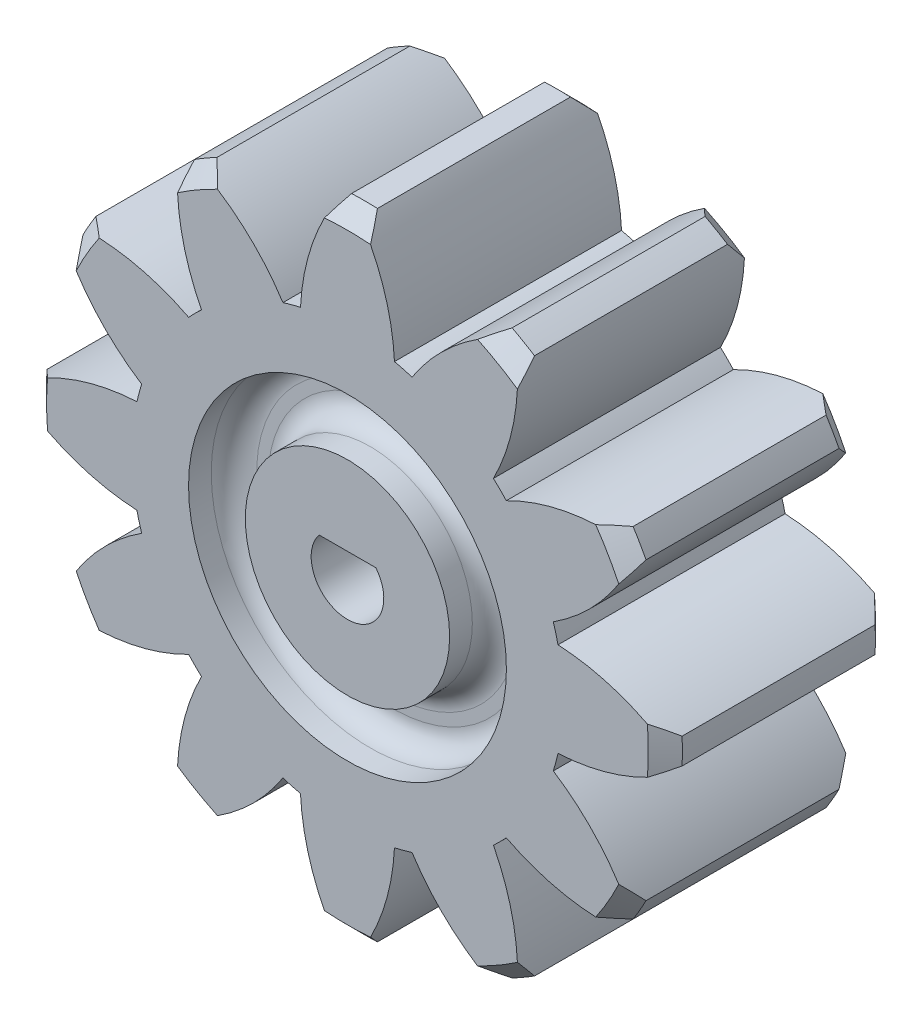
SolidWorks part; units mm, degrees
ref_plane "Front Plane" through (0, 0, 0) normal (0, 0, 1) x (1, 0, 0)
ref_plane "Top Plane" through (0, 0, 0) normal (0, 1, 0) x (1, 0, 0)
ref_plane "Right Plane" through (0, 0, 0) normal (1, 0, 0) x (0, 0, -1)
sketch "Sketch1" plane through (0, 0, 0) normal (0, 0, 1) x (1, 0, 0)
  line L0 (0, 18.2844) -> (0, -18.5063) construction
  line L1 (-21.4042, 0) -> (32.7718, 0) construction
  line L2 (-1.57, 17.3282) -> (-1.57, 3.0678) construction
  line L3 (-0.57, 19.83) -> (-0.57, 2.7238) construction
  line L4 (-2.07, 15.9554) -> (-2.07, 3.2392) construction
  circle A0 centre (0, 0) radius 9.5
  circle A1 centre (0, 0) radius 12 construction
  circle A2 centre (0, 0) radius 14
  arc A3 (-2.07, 9.2717) -> (-0.57, 13.9884) centre (7.6252, 8.7853) cw
  arc A4 (2.07, 9.2717) -> (0.57, 13.9884) centre (-7.6252, 8.7853) ccw
  point P18 (-1.57, 11.8969)
  dimension "D1" = 19
  dimension "D2" = 24
  dimension "D3" = 28
  dimension "D4" = 1.57
  dimension "D5" = 1
  dimension "D6" = 0.5
extrude "Boss-Extrude1" add sketch "Sketch1" along normal blind 10 contours A0 | A0 A4 A2 A3
chamfer "Chamfer1" distance 0.75 angle 45 2 edges at (0, 14, 0) (0, 14, 10)
pattern_circular "CirPattern1" count 12 over 360 about axis through (0, 0, 0) along (0, 0, 1) of "Boss-Extrude1", "Chamfer1"
sketch "Sketch2" plane through (0, 0, 10) normal (0, 0, 1) x (1, 0, 0)
  circle A0 centre (0, 0) radius 7
  circle A1 centre (0, 0) radius 4.5
  dimension "D1" = 14
  dimension "D2" = 9
extrude "Cut-Extrude1" cut sketch "Sketch2" against normal blind 2
fillet "Fillet1" radius 1 2 edges at (7, 0, 8) (4.5, 0, 8)
ref_plane "Plane1" through (0, 0, 5) normal (0, 0, 1) x (1, 0, 0)
mirror "Mirror1" about plane through (0, 0, 5) normal (0, 0, 1) of "Fillet1", "Cut-Extrude1"
sketch "Sketch3" plane through (0, 0, 10) normal (0, 0, 1) x (1, 0, 0)
  line L0 (-1.249, 1) -> (1.249, 1)
  circle A0 centre (0, 0) radius 1.6
  dimension "D1" = 3.2
  dimension "D2" = 2.6
extrude "Cut-Extrude2" cut sketch "Sketch3" against normal up to next contours L0 A0
